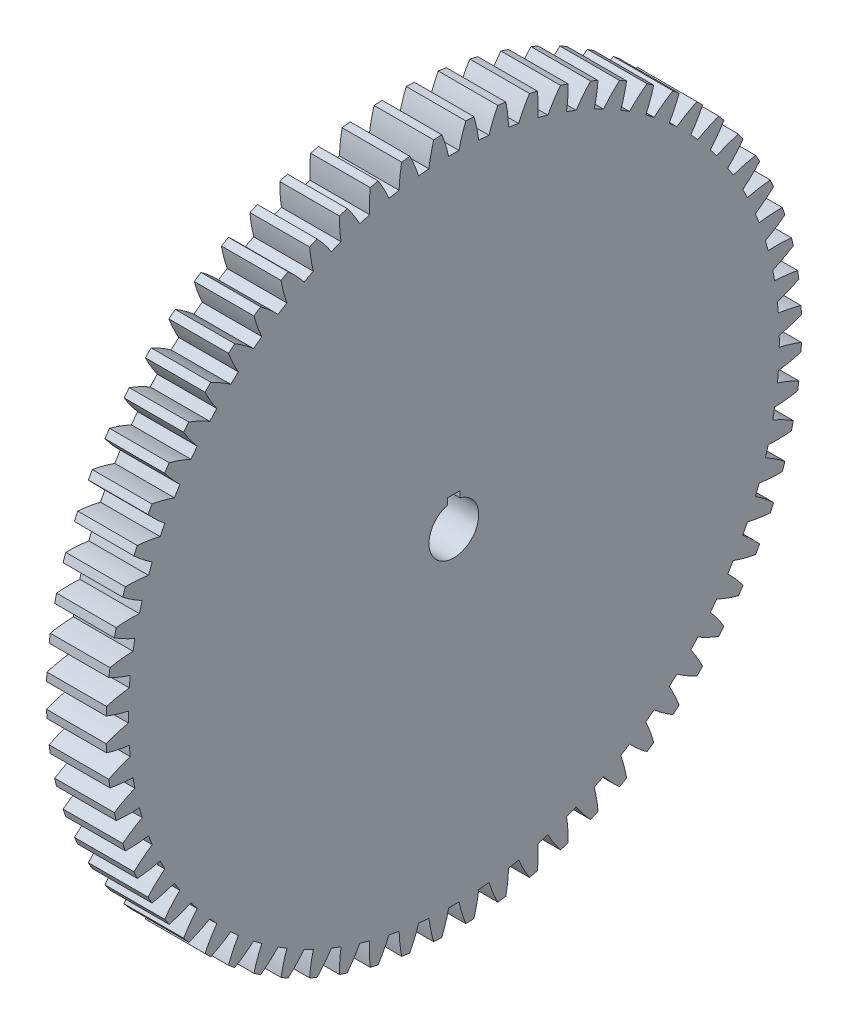
SolidWorks part; units mm, degrees
ref_plane "Plane1" through (0, 0, 0) normal (0, 0, 1) x (1, 0, 0)
ref_plane "Plane2" through (0, 0, 0) normal (0, 1, 0) x (1, 0, 0)
ref_plane "Plane3" through (0, 0, 0) normal (1, 0, 0) x (0, 0, -1)
other "Configuration Table"
sketch "HoldingSke" plane through (0, 0, 0) normal (0, 1, 0) x (1, 0, 0)
  line L0 (0, 0) -> (4.7575, -11.7752)
  line L1 (-15, 0) -> (100, 0) construction
  line L2 (0, 0) -> (-2.1039, 2.3779)
  line L3 (0, 0) -> (-11.863, 4.5341)
  line L4 (0, 0) -> (3.2351, 8.0072)
  line L5 (0, 0) -> (-47.5972, -17.7524)
  line L6 (0, 0) -> (-252.6679, -170.4757)
  line L7 (-2.1039, 2.3779) -> (63.5041, 300.0332)
  line L8 (-76.2, 54.61) -> (205.6384, 54.61)
  line L9 (-67.7845, 28.3722) -> (-49.3413, 33.142)
  line L10 (-76.2, 71.12) -> (104.1128, 71.12)
  line L11 (0, 0) -> (-304.8, 0)
  line L12 (-76.2, 101.6) -> (-74.295, 101.6)
  line L13 (24.9733, 27.94) -> (52.9518, 28.4284)
  line L14 (24.9733, 27.94) -> (24.9746, 27.94)
  line L15 (24.9733, 27.94) -> (100.4006, 29.5858)
  circle A0 centre (0, 0) radius 127
  circle A1 centre (0, 0) radius 38.1
  circle A2 centre (0, 0) radius 38.1
  circle A3 centre (0, 0) radius 127
  dimension "MHD" = 76.2
  dimension "Hub_dia" = 76.2
  dimension "Bore" = 254
  dimension "MBD" = 254
  dimension "Num_teeth" = 68
  dimension "Pitch" = 12.7
  dimension "Overall_len" = 50.8
  dimension "Show_teeth" = 68
  dimension "Thickness" = 304.8
  dimension "OAL" = 304.8001
  dimension "T_dim" = 281.8384
  dimension "Ap" = 14.5
  dimension "H" = 19.05
  dimension "Pitch_radius" = 180.3128
  dimension "Width" = 304.8
  dimension "Backlash" = 1.905
  dimension "Addendum_fac" = 1
  dimension "Dedendum_fac" = 1.25
  dimension "Clearance_fac" = 0.25
  dimension "Dedendum_add" = 0.0013
sketch "BasProSke" plane through (0, 0, 0) normal (0, 1, 0) x (1, 0, 0)
  line L0 (-10, 0) -> (60, 0) construction
  line L1 (0, 0) -> (0, 1778)
  line L2 (0, 0) -> (304.8, 0)
  line L3 (304.8, 0) -> (304.8, 1778)
  line L4 (304.8, 1778) -> (0, 1778)
  dimension "Thickness" = 304.8
  dimension "Diameter" = 3556
revolve "Base-Revolve" add sketch "BasProSke" angle 360 about L0
sketch "TooCutSke" plane through (0, 0, 0) normal (1, 0, 0) x (0, 0, -1)
  line L1 (0, 0) -> (0, 107) construction
  line L2 (0, 0) -> (-43.2283, 1726.659) construction
  line L3 (0, 0) -> (-159.5004, 3449.9409) construction
  line L4 (-43.2283, 1726.659) -> (-79.7502, 1724.9704) construction
  arc A0 (26.4373, 1663.4887) -> (-26.4373, 1663.4887) centre (0, 0) ccw
  arc A1 (61.3545, 1776.9665) -> (-61.3545, 1776.9665) centre (0, 0) ccw
  circle A2 centre (0, 0) radius 1727.2 construction
  circle A3 centre (0, 0) radius 1672.1846 construction
  arc A4 (-26.4373, 1663.4887) -> (-61.3545, 1776.9665) centre (-701.7808, 1517.7961) ccw
  arc A5 (61.3545, 1776.9665) -> (26.4373, 1663.4887) centre (701.7808, 1517.7961) ccw
  dimension "Root_dia" = 3327.3975
  dimension "Overcut_dia" = 3556.0508
  dimension "Pitch_dia" = 3454.4
  dimension "Base_dia" = 3344.3692
  dimension "Flank_rad" = 690.88
  dimension "Half_ang" = 2.647
  dimension "Half_CT" = 36.5609
extrude "ToothCut" cut sketch "TooCutSke" along normal through all
fillet "Breaks" [suppressed] radius 1.016
fillet "RootFillets" [suppressed] radius 12.7013
pattern_circular "TeethCuts" count 68 every 5.294 about axis through (-10, 0, 0) along (1, 0, 0) of "ToothCut", "RootFillets", "Breaks"
sketch "HubNeaOneSke" plane through (0, 0, 0) normal (-1, 0, 0) x (0, 0, 1)
  circle A0 centre (0, 0) radius 38.1
  dimension "Diameter" = 76.2
extrude "HubNearOne" [suppressed] add sketch "HubNeaOneSke" along normal blind 25.4001
sketch "HubNeaBotSke" plane through (0, 0, 0) normal (-1, 0, 0) x (0, 0, 1)
  circle A0 centre (0, 0) radius 38.1
  dimension "Diameter" = 76.2
extrude "HubNearBoth" [suppressed] add sketch "HubNeaBotSke" along normal blind 12.7
ref_plane "FarPln" through (304.8, 0, 0) normal (1, 0, 0) x (0, 0, -1)
sketch "HubFarSke" plane through (304.8, 0, 0) normal (1, 0, 0) x (0, 0, -1)
  circle A0 centre (0, 0) radius 38.1
  dimension "Diameter" = 76.2
extrude "HubFar" [suppressed] add sketch "HubFarSke" along normal blind 12.7
sketch "BorSke" plane through (0, 0, 0) normal (1, 0, 0) x (0, 0, -1)
  circle A0 centre (0, 0) radius 127
  dimension "Diameter" = 254
extrude "Bore" cut sketch "BorSke" along normal mid plane 609.6001
sketch "KeySke" plane through (0, 0, 0) normal (1, 0, 0) x (0, 0, -1)
  line L0 (-31.75, 0) -> (-31.75, 154.8384)
  line L1 (-31.75, 154.8384) -> (31.75, 154.8384)
  line L2 (31.75, 154.8384) -> (31.75, 0)
  line L3 (0, 0) -> (0, 34) construction
  line L4 (-31.75, 0) -> (31.75, 0)
  dimension "Offset" = 154.8384
  dimension "Width" = 63.5
extrude "Keyway" cut sketch "KeySke" along normal mid plane 609.6001
pattern_circular "Keyway2" [suppressed] count 2 every 90 about axis through (-10, 0, 0) along (1, 0, 0)
equation "' \"Pitch@HoldingSke\" = 4"
equation "' \"Num_teeth@HoldingSke\" = 12"
equation "' \"Ap@HoldingSke\" =  20"
equation "' \"Ap@HoldingSke\" = 20"
equation "' \"Width@HoldingSke\" = 0.5"
equation "' \"Hub_dia@HoldingSke\"= 1"
equation "' \"Hub_dia@HoldingSke\" = 1"
equation "' \"Overall_len@HoldingSke\" = 1.0"
equation "' \"Bore@HoldingSke\" = 0.75"
equation "' \"T_dim@HoldingSke\" = 0.85"
equation "' \"Width@KeySke\" = 0.25"
equation "' \"Show_teeth@HoldingSke\" = 13"
equation "' \"Backlash@HoldingSke\" = 0.009"
equation "' \"Addendum_fac@HoldingSke\" = 1.0"
equation "' \"Dedendum_fac@HoldingSke\" = 1.25"
equation "' \"Dedendum_add@HoldingSke\" = 0.00005"
equation "' \"Clearance_fac@HoldingSke\" = 0.25"
equation "' \"Pitch@HoldingSke\" = 0.5"
equation "' \"Num_teeth@HoldingSke\" = 23"
equation "' \"Show_teeth@HoldingSke\" = 23"
equation "' \"Backlash@HoldingSke\" = 0.0375"
equation "\"Overcut_dia@TooCutSke\" = (\"Num_teeth@HoldingSke\" + 2 * \"Addendum_fac@HoldingSke\") / \"Pitch@HoldingSke\" + 0.002"
equation "\"Pitch_dia@TooCutSke\" = \"Num_teeth@HoldingSke\" / \"Pitch@HoldingSke\""
equation "\"Base_dia@TooCutSke\" = \"Num_teeth@HoldingSke\" / \"Pitch@HoldingSke\" * cos((\"Ap@HoldingSke\"  * 3.14159265 / 180))"
equation "\"Root_dia@TooCutSke\" = (\"Num_teeth@HoldingSke\" + 2) / \"Pitch@HoldingSke\" - 2 * (\"Addendum_fac@HoldingSke\" + \"Dedendum_fac@HoldingSke\") / \"Pitch@HoldingSke\" - \"Dedendum_add@HoldingSke\" * 2"
equation "\"Half_ang@TooCutSke\" = 180 / \"Num_teeth@HoldingSke\""
equation "\"Half_CT@TooCutSke\" = \"Num_teeth@HoldingSke\" / \"Pitch@HoldingSke\" * sin((3.14159265 / 2 / \"Num_teeth@HoldingSke\")) / 2 - 7 * \"Backlash@HoldingSke\" / 4"
equation "\"Flank_rad@TooCutSke\" = \"Num_teeth@HoldingSke\" / \"Pitch@HoldingSke\" / 5"
equation "\"Radius@RootFillets\" = \"Clearance_fac@HoldingSke\" / \"Pitch@HoldingSke\" + \"Dedendum_add@HoldingSke\""
equation "\"Break_rad@Breaks\" = 0.02 / \"Pitch@HoldingSke\""
equation "\"Thickness@HoldingSke\" = \"Width@HoldingSke\""
equation "\"OAL@HoldingSke\" = \"Thickness@HoldingSke\""
equation "\"MHD@HoldingSke\" = (\"Num_teeth@HoldingSke\" + 2) / \"Pitch@HoldingSke\" - 2 * (\"Addendum_fac@HoldingSke\" + \"Dedendum_fac@HoldingSke\")  / \"Pitch@HoldingSke\" - \"Dedendum_add@HoldingSke\" * 2"
equation "\"MBD@HoldingSke\" = (\"Num_teeth@HoldingSke\" + 2) / \"Pitch@HoldingSke\" - 2 * (\"Addendum_fac@HoldingSke\" + \"Dedendum_fac@HoldingSke\")  / \"Pitch@HoldingSke\" - \"Dedendum_add@HoldingSke\" * 2 - 0.002"
equation "\"MHD@HoldingSke\" = ((sgn( \"MHD@HoldingSke\" - \"Hub_dia@HoldingSke\" )-1)*( \"MHD@HoldingSke\" - \"Hub_dia@HoldingSke\" ))/-2+ \"Hub_dia@HoldingSke\""
equation "\"MBD@HoldingSke\" = ((sgn( \"MBD@HoldingSke\" - \"Bore@HoldingSke\" )-1)*( \"MBD@HoldingSke\" - \"Bore@HoldingSke\" ))/-2+ \"Bore@HoldingSke\""
equation "\"OAL@HoldingSke\" = ((sgn( \"OAL@HoldingSke\" - \"Overall_len@HoldingSke\" )+1)*( \"OAL@HoldingSke\" - \"Overall_len@HoldingSke\" ))/2 + \"Overall_len@HoldingSke\" + 0.000002"
equation "\"Num_teeth@TeethCuts\" = int( \"Show_teeth@HoldingSke\" ) + 1"
equation "\"Num_teeth@TeethCuts\" = ((sgn( \"Num_teeth@TeethCuts\" - \"Num_teeth@HoldingSke\" )-1)*( \"Num_teeth@TeethCuts\" - \"Num_teeth@HoldingSke\" ))/-2+ \"Num_teeth@HoldingSke\""
equation "\"Num_teeth@TeethCuts\" = ((sgn( \"Num_teeth@TeethCuts\" - 2.0)+1)*( \"Num_teeth@TeethCuts\" - 2.0))/2 +2.0"
equation "\"Angle@TeethCuts\" = 360.0 / \"Num_teeth@HoldingSke\""
equation "\"Diameter@BasProSke\" = (\"Num_teeth@HoldingSke\" + 2 * \"Addendum_fac@HoldingSke\") / \"Pitch@HoldingSke\""
equation "\"Thickness@BasProSke\"  = \"Thickness@HoldingSke\""
equation "' \"Fillet_rad@BasProSke\" =  \"Thickness@HoldingSke\" * 0.05"
equation "' \"Fillet_rad@BasProSke\" = \"Thickness@HoldingSke\" * 0.05"
equation "\"MHD@HoldingSke\" = ((sgn( \"MHD@HoldingSke\" - \"Root_dia@TooCutSke\" )-1)*( \"MHD@HoldingSke\" - \"Root_dia@TooCutSke\" ))/-2+ \"Root_dia@TooCutSke\""
equation "\"Diameter@HubNeaOneSke\" = \"MHD@HoldingSke\""
equation "\"Length@HubNearOne\" = \"OAL@HoldingSke\" - \"Thickness@BasProSke\""
equation "\"Diameter@HubNeaBotSke\" = \"MHD@HoldingSke\""
equation "\"Length@HubNearBoth\" = ( \"OAL@HoldingSke\" - \"Thickness@BasProSke\" ) / 2.0"
equation "\"Thickness@FarPln\" = \"Thickness@BasProSke\""
equation "\"Diameter@HubFarSke\" = \"MHD@HoldingSke\""
equation "\"Length@HubFar\" = ( \"OAL@HoldingSke\" - \"Thickness@BasProSke\" ) / 2.0"
equation "\"Diameter@BorSke\" = \"MBD@HoldingSke\""
equation "\"D1@Bore\" = \"OAL@HoldingSke\" * 2.0"
equation "\"D1@Keyway\" = \"OAL@HoldingSke\" * 2.0"
equation "\"Offset@KeySke\" = \"T_dim@HoldingSke\" - \"MBD@HoldingSke\" / 2.0"
